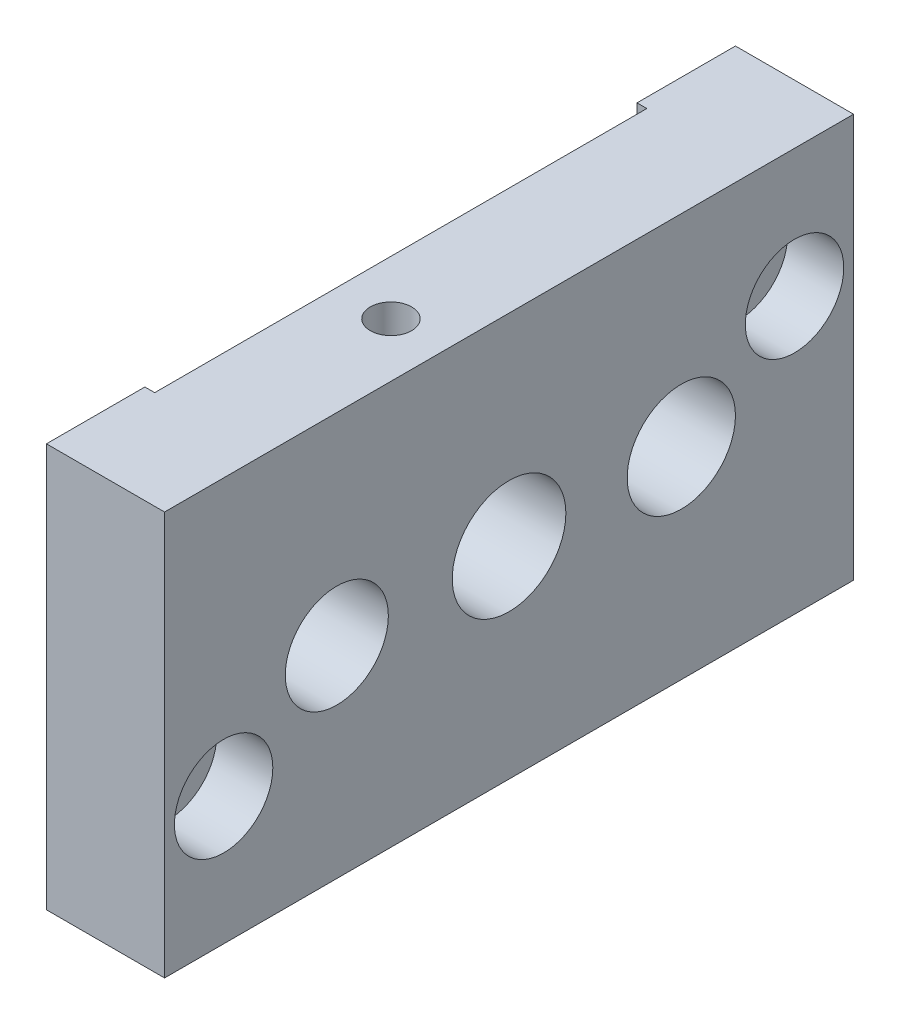
SolidWorks part; units mm, degrees
ref_plane "Front Plane" through (0, 0, 0) normal (0, 0, 1) x (1, 0, 0)
ref_plane "Top Plane" through (0, 0, 0) normal (0, 1, 0) x (1, 0, 0)
ref_plane "Right Plane" through (0, 0, 0) normal (1, 0, 0) x (0, 0, -1)
sketch "Sketch1" plane through (0, 0, 0) normal (0, 1, 0) x (1, 0, 0)
  line L0 (-6, 25) -> (-5, 25)
  line L1 (-6, -35) -> (6, -35)
  line L2 (-6, -35) -> (-6, -25)
  line L3 (-6, 35) -> (6, 35)
  line L4 (6, -35) -> (6, 35)
  line L5 (-6, -35) -> (6, 35) construction
  line L6 (-6, 35) -> (6, -35) construction
  line L7 (-5, 25) -> (-5, -25)
  line L8 (-5, -25) -> (-6, -25)
  line L9 (-6, 25) -> (-6, 35)
  point P0 (0, 0)
  dimension "D1" = 12
  dimension "D2" = 70
  dimension "D3" = 10
  dimension "D4" = 10
  dimension "D5" = 1
extrude "Boss-Extrude1" add sketch "Sketch1" along normal blind 41
sketch "Sketch2" plane through (6, 0, 0) normal (1, 0, 0) x (0, 0, -1)
  line L0 (-35, 41) -> (-35, 0) construction
  line L1 (-35, 0) -> (35, 0) construction
  line L2 (-35, 41) -> (35, 41) construction
  circle A1 centre (29, 28) radius 2.75
  circle A2 centre (-17.5, 20.5) radius 5.2371
  circle A3 centre (0, 20.5) radius 5.7713
  circle A4 centre (17.5, 20.5) radius 5.5
  circle A5 centre (-29, 13) radius 2.75
  point P14 (0, 0)
  dimension "D7" = 13
  dimension "D9" = 5.5
  dimension "D10" = 5.5
  dimension "D11" = 11
  dimension "D12" = 10.4742
  dimension "D1" = 64
  dimension "D2" = 35
  dimension "D3" = 17.5
  dimension "D4" = 17.5
  dimension "D5" = 6
  dimension "D6" = 17.5
  dimension "D8" = 13
extrude "Cut-Extrude10" cut sketch "Sketch2" against normal through all contours A2 | A3 | A4 | A1 | A5
sketch "Sketch11" plane through (6, 0, 0) normal (1, 0, 0) x (0, 0, -1)
  circle A0 centre (29, 28) radius 5
  circle A1 centre (-29, 13) radius 5
extrude "Cut-Extrude11" cut sketch "Sketch11" against normal blind 5.7 contours A1 | A0
hole_wizard "M5 Tapped Hole1" positions "Sketch12" profile "Sketch13" tap size "M5" standard "DIN"
sketch "Sketch12" plane through (0, 41, 0) normal (0, 1, 0) x (1, 0, 0)
  line L0 (6, -35) -> (6, 35) construction
  line L1 (-6, -35) -> (6, -35) construction
  point P0 (0.5, -6.5)
  dimension "D1" = 5.5
  dimension "D2" = 28.5
sketch "Sketch13" plane through (0.5, 41, 6.5) normal (1, 0, 0) x (0, 0, 1)
  line L0 (0, 0) -> (0, 13.2618)
  line L1 (0, 13.2618) -> (2.1, 12)
  line L2 (2.1, 12) -> (2.1, 0)
  line L5 (2.1, 0) -> (0, 0)
  line L10 (0, 13.2618) -> (-2.1, 12) construction
  line L11 (0, -6.35) -> (0, 107.95) construction
  dimension "Tap Drill Dia." = 4.2
  dimension "Tap Drill Depth" = 12
  dimension "Drill Angle" = 118
cosmetic thread "Hole Thread1" parameters "D1"=10, "D2"=5
